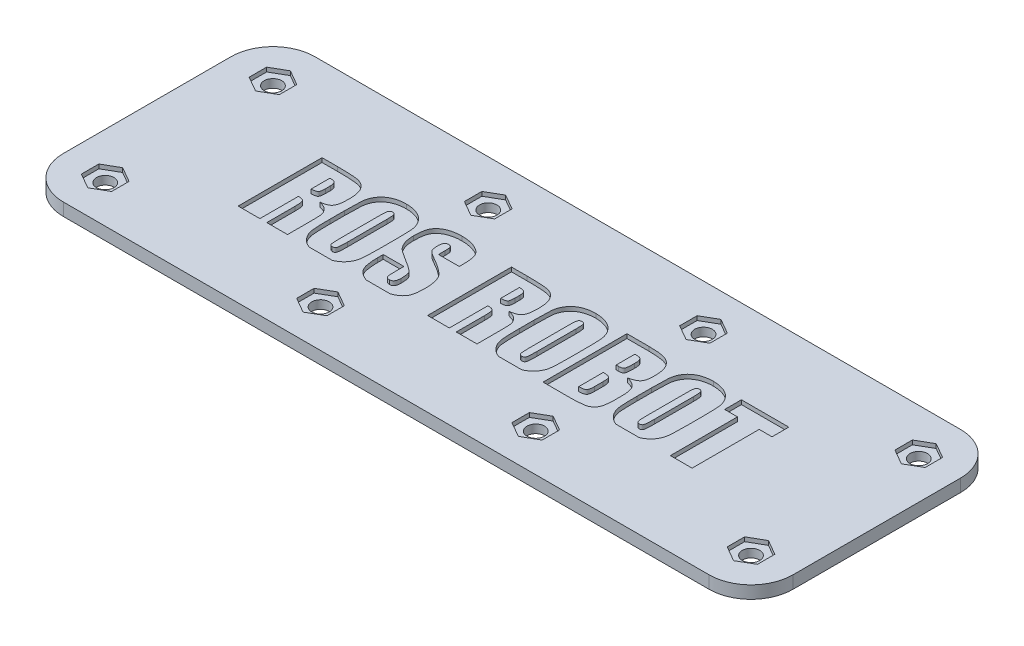
SolidWorks part; units mm, degrees
ref_plane "Front Plane" through (0, 0, 0) normal (0, 0, 1) x (1, 0, 0)
ref_plane "Top Plane" through (0, 0, 0) normal (0, 1, 0) x (1, 0, 0)
ref_plane "Right Plane" through (0, 0, 0) normal (1, 0, 0) x (0, 0, -1)
sketch "Sketch1" plane through (0, 0, 0) normal (0, 1, 0) x (1, 0, 0)
  line L1 (-87, 30) -> (87, 30)
  line L2 (-87, 30) -> (-87, -30)
  line L3 (-87, -30) -> (87, -30)
  line L4 (87, 30) -> (87, -30)
  line L5 (-87, 30) -> (87, -30) construction
  line L6 (-87, -30) -> (87, 30) construction
  point P0 (0, 0)
  dimension "D1" = 60
  dimension "D2" = 174
extrude "Boss-Extrude1" add sketch "Sketch1" along normal blind 3
sketch "Sketch2" plane through (0, 3, 0) normal (0, 1, 0) x (1, 0, 0)
  line L0 (-87, 30) -> (-87, -30) construction
  circle A0 centre (-76.995, 20) radius 2.09
  circle A1 centre (-25.665, 20) radius 2.09
  circle A2 centre (25.665, 20) radius 2.09
  circle A3 centre (76.995, 20) radius 2.09
  dimension "D1" = 4.18
  dimension "D2" = 4
  dimension "D3" = 10.005
  dimension "D4" = 20
extrude "Cut-Extrude1" cut sketch "Sketch2" against normal through all
mirror "Mirror1" about plane through (0, 0, 0) normal (0, 0, 1) of "Cut-Extrude1"
fillet "Fillet1" radius 10 4 edges at (-87, 1.5, 30) (87, 1.5, 30) (87, 1.5, -30) (-87, 1.5, -30)
sketch "Sketch3" plane through (0, 3, 0) normal (0, 1, 0) x (1, 0, 0)
  line L0 (-70, -10) -> (70, -10)
  line L1 (-55.2941, 10) -> (-51.5662, 10)
  line L2 (-43.5294, -4.6581) -> (-43.5294, -10)
  line L3 (-43.5294, -10) -> (-48.4706, -10)
  line L4 (-48.4706, -10) -> (-48.4706, -3.2353)
  line L5 (-50.1176, -0.8235) -> (-50.1176, -10)
  line L6 (-50.1176, -10) -> (-55.2941, -10)
  line L7 (-55.2941, -10) -> (-55.2941, 10)
  line L8 (-50.1176, 6.7059) -> (-50.1176, 2.2353)
  line L9 (-48.4706, 4.0478) -> (-48.4706, 5.1544)
  line L10 (-41.6471, -1.7206) -> (-41.6471, 1.7206)
  line L11 (-29.6471, 1.7206) -> (-29.6471, -1.7206)
  line L12 (-36.4706, 4.9596) -> (-36.4706, -4.5662)
  line L13 (-34.8235, -4.4154) -> (-34.8235, 4.9596)
  line L14 (-16.4706, 3.8824) -> (-21.4118, 3.8824)
  line L15 (-21.4118, 3.8824) -> (-21.4118, 5.4632)
  line L16 (-28, -4.0478) -> (-28, -2.7059)
  line L17 (-28, -2.7059) -> (-23.0588, -2.7059)
  line L18 (-23.0588, -2.7059) -> (-23.0588, -5.2978)
  line L19 (-16.4706, 4.6875) -> (-16.4706, 3.8824)
  line L20 (-10.1176, 10) -> (-6.3897, 10)
  line L21 (1.6471, -4.6581) -> (1.6471, -10)
  line L22 (1.6471, -10) -> (-3.2941, -10)
  line L23 (-3.2941, -10) -> (-3.2941, -3.2353)
  line L24 (-4.9412, -0.8235) -> (-4.9412, -10)
  line L25 (-4.9412, -10) -> (-10.1176, -10)
  line L26 (-10.1176, -10) -> (-10.1176, 10)
  line L27 (-4.9412, 6.7059) -> (-4.9412, 2.2353)
  line L28 (-3.2941, 4.0478) -> (-3.2941, 5.1544)
  line L29 (3.5294, -1.7206) -> (3.5294, 1.7206)
  line L30 (15.5294, 1.7206) -> (15.5294, -1.7206)
  line L31 (8.7059, 4.9596) -> (8.7059, -4.5662)
  line L32 (10.3529, -4.4154) -> (10.3529, 4.9596)
  line L33 (17.4118, 10) -> (22.7169, 10)
  line L34 (29.6471, -3.364) -> (29.6471, -5.2426)
  line L35 (23.4926, -10) -> (17.4118, -10)
  line L36 (17.4118, -10) -> (17.4118, 10)
  line L37 (22.5882, 6.7059) -> (22.5882, 2.2353)
  line L38 (22.5882, -0.8235) -> (22.5882, -6.7059)
  line L39 (24.4706, -4.7463) -> (24.4706, -2.7831)
  line L40 (31.5294, -1.7206) -> (31.5294, 1.7206)
  line L41 (43.5294, 1.7206) -> (43.5294, -1.7206)
  line L42 (36.7059, 4.9596) -> (36.7059, -4.5662)
  line L43 (38.3529, -4.4154) -> (38.3529, 4.9596)
  line L44 (56, 10) -> (56, 6)
  line L45 (56, 6) -> (52.9412, 6)
  line L46 (52.9412, 6) -> (52.9412, -10)
  line L47 (52.9412, -10) -> (47.7647, -10)
  line L48 (47.7647, -10) -> (47.7647, 6)
  line L49 (47.7647, 6) -> (44.7059, 6)
  line L50 (44.7059, 6) -> (44.7059, 10)
  line L51 (44.7059, 10) -> (56, 10)
  spline S0 degree 3 poles (-51.5662, 10) (-50.9938, 10.0021) (-50.1738, 9.9925) (-49.131, 9.9618) (-48.4616, 9.9343) (-47.8671, 9.8938) (-47.3485, 9.8469) (-46.9053, 9.7938) (-46.5265, 9.7279) (-46.1927, 9.6422) (-45.8846, 9.5296) (-45.5898, 9.3956) (-45.3117, 9.2282) (-45.0523, 9.0316) (-44.8023, 8.8156) (-44.5748, 8.5646) (-44.3559, 8.2904) (-44.158, 7.9777) (-43.9907, 7.6226) (-43.847, 7.2263) (-43.7305, 6.7869) (-43.6403, 6.3051) (-43.5478, 5.579) (-43.5348, 5.0099) (-43.5294, 4.6176) knots 0 0 0 0 0.148881 0.213303 0.271377 0.323138 0.368276 0.406827 0.439217 0.468212 0.496346 0.524443 0.552325 0.580569 0.609028 0.638128 0.668547 0.700209 0.734143 0.770448 0.80973 0.852244 0.897872 1 1 1 1
  spline S1 degree 3 poles (-43.5294, 4.6176) (-43.5236, 4.2653) (-43.5474, 3.7599) (-43.6025, 3.1182) (-43.671, 2.7076) (-43.7489, 2.3431) (-43.8469, 2.023) (-43.9667, 1.7514) (-44.1058, 1.5209) (-44.2744, 1.3269) (-44.4747, 1.1564) (-44.7132, 1.0108) (-44.9842, 0.8814) (-45.2896, 0.7718) (-45.7649, 0.6509) (-46.1435, 0.5949) (-46.4081, 0.5735) knots 0 0 0 0 0.18379 0.264137 0.336087 0.400976 0.458649 0.510492 0.555595 0.598692 0.64408 0.692369 0.744168 0.800637 0.861472 1 1 1 1
  spline S2 degree 3 poles (-46.4081, 0.5735) (-46.1692, 0.5082) (-45.8228, 0.4157) (-45.3924, 0.2537) (-45.1176, 0.1239) (-44.8709, -0.0075) (-44.6579, -0.1504) (-44.475, -0.3016) (-44.2801, -0.5089) (-44.0843, -0.7699) (-43.8891, -1.0747) (-43.748, -1.3697) (-43.6652, -1.6199) (-43.6287, -1.8463) (-43.5978, -2.0715) (-43.5791, -2.3577) (-43.5604, -2.7033) (-43.5466, -3.1078) (-43.5296, -3.7658) (-43.5348, -4.2893) (-43.5294, -4.6581) knots 0 0 0 0 0.11023 0.159227 0.204341 0.24532 0.283418 0.318243 0.350629 0.40972 0.463107 0.511383 0.554826 0.57974 0.613275 0.655917 0.707227 0.767226 0.835926 1 1 1 1
  spline S3 degree 3 poles (-48.4706, -3.2353) (-48.4728, -2.9891) (-48.4724, -2.639) (-48.5052, -2.1981) (-48.5325, -1.9256) (-48.5697, -1.6913) (-48.6105, -1.4957) (-48.6657, -1.339) (-48.7289, -1.2146) (-48.8113, -1.114) (-48.9232, -1.039) (-49.055, -0.9678) (-49.2166, -0.9133) (-49.4044, -0.8752) (-49.7069, -0.834) (-49.9484, -0.8249) (-50.1176, -0.8235) knots 0 0 0 0 0.208712 0.296135 0.374434 0.440653 0.497065 0.543362 0.580978 0.614872 0.652041 0.694298 0.741574 0.795735 0.856514 1 1 1 1
  spline S4 degree 3 poles (-50.1176, 2.2353) (-49.8576, 2.2338) (-49.4959, 2.2542) (-49.0697, 2.3585) (-48.8674, 2.4456) (-48.7457, 2.5571) (-48.6674, 2.6702) (-48.6082, 2.8204) (-48.5571, 3.0015) (-48.5182, 3.2158) (-48.4758, 3.5672) (-48.4762, 3.8494) (-48.4706, 4.0478) knots 0 0 0 0 0.26319 0.361521 0.442778 0.481273 0.526535 0.580255 0.643242 0.716208 0.799609 1 1 1 1
  spline S5 degree 3 poles (-48.4706, 5.1544) (-48.4732, 5.4183) (-48.4915, 5.7882) (-48.649, 6.209) (-48.8134, 6.422) (-49.0502, 6.5523) (-49.4796, 6.6913) (-49.8538, 6.7008) (-50.1176, 6.7059) knots 0 0 0 0 0.296724 0.405999 0.497474 0.590179 0.702697 1 1 1 1
  spline S6 degree 3 poles (-29.6471, -1.7206) (-29.6515, -2.1875) (-29.649, -2.8616) (-29.6628, -3.7232) (-29.6839, -4.2868) (-29.699, -4.7944) (-29.7259, -5.2478) (-29.7546, -5.6462) (-29.7961, -6.1016) (-29.8819, -6.6249) (-30.0686, -7.2195) (-30.3331, -7.7852) (-30.6652, -8.3214) (-31.0707, -8.8126) (-31.5464, -9.2461) (-32.0877, -9.6199) (-32.694, -9.9286) (-33.3578, -10.1686) (-34.3389, -10.4147) (-35.1174, -10.4641) (-35.6471, -10.4706) knots 0 0 0 0 0.112809 0.162854 0.208179 0.249065 0.285542 0.317902 0.345566 0.396043 0.445676 0.495616 0.546553 0.597656 0.649001 0.701564 0.75612 0.812885 0.871769 1 1 1 1
  spline S7 degree 3 poles (-35.6471, -10.4706) (-36.157, -10.4718) (-36.9063, -10.4086) (-37.8652, -10.1914) (-38.5237, -9.9594) (-39.1336, -9.6653) (-39.6789, -9.2941) (-40.1716, -8.8683) (-40.5862, -8.3693) (-40.9353, -7.8326) (-41.2061, -7.2648) (-41.3995, -6.6755) (-41.4957, -6.1587) (-41.5357, -5.7074) (-41.565, -5.3091) (-41.59, -4.8519) (-41.6129, -4.3384) (-41.6259, -3.766) (-41.6415, -2.8873) (-41.6458, -2.1985) (-41.6471, -1.7206) knots 0 0 0 0 0.123179 0.180929 0.237119 0.291548 0.344027 0.396062 0.448383 0.50021 0.550408 0.599943 0.649656 0.677029 0.709392 0.746168 0.787661 0.833574 0.884513 1 1 1 1
  spline S8 degree 3 poles (-41.6471, 1.7206) (-41.6425, 2.1887) (-41.6454, 2.8628) (-41.6311, 3.7244) (-41.6108, 4.2868) (-41.5934, 4.7954) (-41.5734, 5.2491) (-41.5426, 5.6473) (-41.5025, 6.102) (-41.4109, 6.6245) (-41.2257, 7.2194) (-40.9622, 7.7848) (-40.6264, 8.3182) (-40.225, 8.8141) (-39.7442, 9.2434) (-39.2063, 9.6217) (-38.599, 9.9269) (-37.9368, 10.1755) (-36.9518, 10.4071) (-36.1771, 10.476) (-35.6471, 10.4706) knots 0 0 0 0 0.1131 0.162847 0.20817 0.249054 0.28581 0.317873 0.345536 0.396062 0.445693 0.495631 0.546315 0.597643 0.649205 0.701523 0.756077 0.812942 0.872041 1 1 1 1
  spline S9 degree 3 poles (-35.6471, 10.4706) (-35.1376, 10.4697) (-34.3878, 10.4128) (-33.4319, 10.1862) (-32.7748, 9.9554) (-32.1629, 9.6647) (-31.6159, 9.2964) (-31.1263, 8.8668) (-30.7111, 8.3696) (-30.3634, 7.8316) (-30.0871, 7.2658) (-29.8946, 6.6743) (-29.798, 6.1563) (-29.7599, 5.7048) (-29.7225, 5.3082) (-29.7063, 4.8517) (-29.6803, 4.3385) (-29.6698, 3.7659) (-29.6434, 2.8875) (-29.6546, 2.1984) (-29.6471, 1.7206) knots 0 0 0 0 0.123202 0.180743 0.236944 0.291253 0.343988 0.395811 0.448142 0.499979 0.550314 0.59986 0.649873 0.677251 0.709348 0.746116 0.787617 0.833538 0.884493 1 1 1 1
  spline S10 degree 3 poles (-34.8235, 4.9596) (-34.8242, 5.1753) (-34.83, 5.4829) (-34.843, 5.8716) (-34.8622, 6.1155) (-34.8839, 6.3276) (-34.9074, 6.5086) (-34.9406, 6.6559) (-34.9862, 6.806) (-35.0702, 6.954) (-35.2687, 7.1431) (-35.486, 7.1725) (-35.6213, 7.1765) knots 0 0 0 0 0.245382 0.350014 0.44228 0.523563 0.592561 0.649714 0.69512 0.770679 0.840726 1 1 1 1
  spline S11 degree 3 poles (-35.6213, 7.1765) (-35.7476, 7.1828) (-35.9326, 7.1386) (-36.1407, 7.0007) (-36.2446, 6.8771) (-36.3135, 6.7446) (-36.354, 6.6034) (-36.3908, 6.4253) (-36.4175, 6.2075) (-36.4453, 5.9516) (-36.4612, 5.5307) (-36.473, 5.1963) (-36.4706, 4.9596) knots 0 0 0 0 0.141273 0.207934 0.278501 0.320511 0.375555 0.443281 0.525523 0.622695 0.733336 1 1 1 1
  spline S12 degree 3 poles (-36.4706, -4.5662) (-36.4661, -4.8346) (-36.4689, -5.2158) (-36.4552, -5.6951) (-36.4341, -5.9902) (-36.4194, -6.2432) (-36.3928, -6.4541) (-36.365, -6.6225) (-36.3252, -6.7864) (-36.2427, -6.9456) (-36.032, -7.1431) (-35.8027, -7.1757) (-35.6581, -7.1765) knots 0 0 0 0 0.263966 0.37491 0.47152 0.554902 0.624119 0.680394 0.722784 0.789642 0.853612 1 1 1 1
  spline S13 degree 3 poles (-35.6581, -7.1765) (-35.5065, -7.1791) (-35.2706, -7.1295) (-35.0575, -6.9077) (-34.9787, -6.7275) (-34.9317, -6.5458) (-34.9057, -6.3632) (-34.8796, -6.1401) (-34.8574, -5.8753) (-34.8447, -5.5687) (-34.8286, -5.0773) (-34.825, -4.6887) (-34.8235, -4.4154) knots 0 0 0 0 0.145036 0.209347 0.281953 0.327187 0.385478 0.455017 0.538188 0.634996 0.743262 1 1 1 1
  spline S14 degree 3 poles (-21.4118, 5.4632) (-21.4127, 5.7647) (-21.4197, 6.1714) (-21.5052, 6.6431) (-21.5927, 6.8638) (-21.7193, 7.0116) (-21.938, 7.1462) (-22.1365, 7.1803) (-22.2721, 7.1765) knots 0 0 0 0 0.412843 0.553103 0.65361 0.73318 0.814494 1 1 1 1
  spline S15 degree 3 poles (-22.2721, 7.1765) (-22.4224, 7.1753) (-22.6526, 7.1339) (-22.8986, 6.9564) (-23.0494, 6.7779) (-23.1638, 6.5473) (-23.267, 6.1427) (-23.3007, 5.8109) (-23.2941, 5.5735) knots 0 0 0 0 0.212113 0.312859 0.418563 0.535756 0.66915 1 1 1 1
  spline S16 degree 3 poles (-23.2941, 5.5735) (-23.2963, 5.2685) (-23.2666, 4.7355) (-23.1434, 4.2139) (-23.0441, 4.0074) knots 0 0 0 0 0.572651 1 1 1 1
  spline S17 degree 3 poles (-23.0441, 4.0074) (-22.9953, 3.9087) (-22.892, 3.7635) (-22.7165, 3.5783) (-22.5391, 3.4317) (-22.3344, 3.2741) (-21.9996, 3.0492) (-21.7223, 2.8928) (-21.5294, 2.7831) knots 0 0 0 0 0.166753 0.269572 0.387216 0.516182 0.662459 1 1 1 1
  spline S18 degree 3 poles (-21.5294, 2.7831) (-20.9703, 2.4734) (-20.1729, 2.0184) (-19.1897, 1.3881) (-18.5738, 0.9563) (-18.0389, 0.5522) (-17.4805, 0.0677) (-17.1194, -0.3024) (-16.9375, -0.5662) knots 0 0 0 0 0.335278 0.4813 0.612364 0.729739 0.832713 1 1 1 1
  spline S19 degree 3 poles (-16.9375, -0.5662) (-16.77, -0.806) (-16.5589, -1.2115) (-16.3573, -1.8106) (-16.226, -2.3243) (-16.1237, -2.8906) (-16.0244, -3.7446) (-16, -4.4137) (-16, -4.875) knots 0 0 0 0 0.195997 0.304678 0.423526 0.551406 0.690506 1 1 1 1
  spline S20 degree 3 poles (-16, -4.875) (-15.998, -5.2123) (-16.0141, -5.701) (-16.0695, -6.3269) (-16.1225, -6.7434) (-16.1969, -7.1236) (-16.2837, -7.469) (-16.3859, -7.7809) (-16.5079, -8.061) (-16.6548, -8.3173) (-16.8301, -8.5575) (-17.0323, -8.7896) (-17.2656, -9.0103) (-17.5281, -9.2213) (-17.8225, -9.4176) (-18.1454, -9.6065) (-18.6171, -9.8482) (-19.2609, -10.0984) (-20.3935, -10.3986) (-21.2929, -10.4667) (-21.9044, -10.4706) knots 0 0 0 0 0.107307 0.155459 0.199907 0.240819 0.278648 0.313174 0.345124 0.37569 0.406967 0.439576 0.4735 0.509002 0.546638 0.58596 0.627987 0.715167 0.805112 1 1 1 1
  spline S21 degree 3 poles (-21.9044, -10.4706) (-22.2484, -10.4757) (-22.7548, -10.4446) (-23.4141, -10.3628) (-23.8804, -10.2732) (-24.328, -10.1612) (-24.7555, -10.0192) (-25.1658, -9.8605) (-25.5494, -9.6676) (-25.9093, -9.4591) (-26.2396, -9.2368) (-26.5368, -8.9991) (-26.8027, -8.7496) (-27.0363, -8.4842) (-27.2339, -8.2027) (-27.4071, -7.9126) (-27.5395, -7.5995) (-27.6487, -7.2653) (-27.7465, -6.9026) (-27.8193, -6.5061) (-27.8876, -6.0774) (-27.9373, -5.6159) (-27.9879, -4.936) (-27.9998, -4.4094) (-28, -4.0478) knots 0 0 0 0 0.100145 0.147666 0.193464 0.238409 0.281993 0.324627 0.366464 0.406944 0.445764 0.482345 0.517706 0.551866 0.585155 0.617796 0.650099 0.683973 0.720175 0.759459 0.801374 0.84664 0.894618 1 1 1 1
  spline S22 degree 3 poles (-23.0588, -5.2978) (-23.0613, -5.4794) (-23.049, -5.7378) (-23.0335, -6.0657) (-23.0047, -6.2711) (-22.98, -6.4517) (-22.9371, -6.6031) (-22.8953, -6.7301) (-22.8277, -6.8628) (-22.7117, -6.9937) (-22.4544, -7.1506) (-22.2151, -7.1729) (-22.0551, -7.1765) knots 0 0 0 0 0.221449 0.31586 0.400263 0.474516 0.538003 0.591926 0.637412 0.719013 0.801608 1 1 1 1
  spline S23 degree 3 poles (-22.0551, -7.1765) (-21.8855, -7.181) (-21.6369, -7.1297) (-21.3606, -6.9481) (-21.2049, -6.755) (-21.0818, -6.5138) (-20.9682, -6.0948) (-20.9412, -5.7502) (-20.9412, -5.5074) knots 0 0 0 0 0.223296 0.324627 0.430189 0.546596 0.679609 1 1 1 1
  spline S24 degree 3 poles (-20.9412, -5.5074) (-20.9409, -5.2301) (-20.9533, -4.8334) (-21.0013, -4.3304) (-21.0575, -4.013) (-21.1206, -3.7324) (-21.2279, -3.4321) (-21.3302, -3.2311) (-21.4228, -3.125) knots 0 0 0 0 0.336674 0.481824 0.613234 0.728042 0.830673 1 1 1 1
  spline S25 degree 3 poles (-21.4228, -3.125) (-21.528, -3.0068) (-21.7234, -2.8316) (-22.0286, -2.599) (-22.3207, -2.3816) (-22.6652, -2.1468) (-23.2182, -1.7846) (-23.6661, -1.5149) (-23.9779, -1.3235) knots 0 0 0 0 0.151175 0.250667 0.367276 0.49971 0.649705 1 1 1 1
  spline S26 degree 3 poles (-23.9779, -1.3235) (-24.2945, -1.1313) (-24.7469, -0.8536) (-25.3157, -0.487) (-25.6766, -0.2459) (-25.9964, -0.028) (-26.2707, 0.1697) (-26.5041, 0.3453) (-26.7572, 0.5568) (-27.0307, 0.8386) (-27.3222, 1.2196) (-27.5825, 1.6572) (-27.8168, 2.1499) (-28.0109, 2.7079) (-28.187, 3.5918) (-28.2419, 4.2954) (-28.2353, 4.7868) knots 0 0 0 0 0.139497 0.199929 0.25485 0.30299 0.345648 0.382207 0.412998 0.469794 0.529711 0.593278 0.661207 0.734924 0.815133 1 1 1 1
  spline S27 degree 3 poles (-28.2353, 4.7868) (-28.2299, 5.1483) (-28.2229, 5.6721) (-28.1555, 6.342) (-28.0911, 6.7866) (-28.0062, 7.1929) (-27.9063, 7.5618) (-27.7803, 7.8893) (-27.6392, 8.183) (-27.4744, 8.4486) (-27.2854, 8.6932) (-27.0793, 8.9296) (-26.8428, 9.1431) (-26.5869, 9.3479) (-26.3089, 9.5388) (-26.0053, 9.711) (-25.5665, 9.9259) (-24.9651, 10.1466) (-23.8851, 10.4114) (-23.0241, 10.4702) (-22.4338, 10.4706) knots 0 0 0 0 0.115094 0.16642 0.214115 0.25793 0.298418 0.335563 0.369391 0.401957 0.434786 0.46765 0.501588 0.535991 0.571894 0.608743 0.64693 0.727243 0.81197 1 1 1 1
  spline S28 degree 3 poles (-22.4338, 10.4706) (-22.0994, 10.4657) (-21.6053, 10.4579) (-20.9648, 10.377) (-20.5106, 10.312) (-20.0772, 10.2133) (-19.6613, 10.1018) (-19.2659, 9.965) (-18.8924, 9.8068) (-18.5432, 9.6352) (-18.2193, 9.4575) (-17.9337, 9.2583) (-17.6686, 9.0613) (-17.4461, 8.8391) (-17.2428, 8.617) (-17.0786, 8.377) (-16.9405, 8.1223) (-16.8309, 7.8384) (-16.7307, 7.5198) (-16.6529, 7.1549) (-16.5815, 6.7482) (-16.5328, 6.2949) (-16.4819, 5.6039) (-16.471, 5.0626) (-16.4706, 4.6875) knots 0 0 0 0 0.103081 0.151694 0.198641 0.244219 0.288419 0.331125 0.37288 0.413199 0.450863 0.486435 0.520313 0.552325 0.583055 0.612876 0.641566 0.672036 0.706398 0.744284 0.786764 0.83346 0.884523 1 1 1 1
  spline S29 degree 3 poles (-6.3897, 10) (-5.8173, 10.0021) (-4.9973, 9.9925) (-3.9545, 9.9618) (-3.2851, 9.9343) (-2.6907, 9.8938) (-2.172, 9.8469) (-1.7288, 9.7938) (-1.3501, 9.7279) (-1.0162, 9.6422) (-0.7081, 9.5296) (-0.4133, 9.3956) (-0.1353, 9.2282) (0.1241, 9.0316) (0.3741, 8.8156) (0.6016, 8.5646) (0.8205, 8.2904) (1.0184, 7.9777) (1.1858, 7.6226) (1.3294, 7.2263) (1.4459, 6.7869) (1.5362, 6.3051) (1.6287, 5.579) (1.6416, 5.0099) (1.6471, 4.6176) knots 0 0 0 0 0.148881 0.213303 0.271377 0.323138 0.368276 0.406827 0.439217 0.468212 0.496346 0.524443 0.552325 0.580569 0.609028 0.638128 0.668547 0.700209 0.734143 0.770448 0.80973 0.852244 0.897872 1 1 1 1
  spline S30 degree 3 poles (1.6471, 4.6176) (1.6529, 4.2653) (1.629, 3.7599) (1.574, 3.1182) (1.5054, 2.7076) (1.4275, 2.3431) (1.3296, 2.023) (1.2098, 1.7514) (1.0707, 1.5209) (0.9021, 1.3269) (0.7018, 1.1564) (0.4633, 1.0108) (0.1923, 0.8814) (-0.1131, 0.7718) (-0.5885, 0.6509) (-0.9671, 0.5949) (-1.2316, 0.5735) knots 0 0 0 0 0.18379 0.264137 0.336087 0.400976 0.458649 0.510492 0.555595 0.598692 0.64408 0.692369 0.744168 0.800637 0.861472 1 1 1 1
  spline S31 degree 3 poles (-1.2316, 0.5735) (-0.9927, 0.5082) (-0.6463, 0.4157) (-0.2159, 0.2537) (0.0589, 0.1239) (0.3056, -0.0075) (0.5186, -0.1504) (0.7015, -0.3016) (0.8963, -0.5089) (1.0921, -0.7699) (1.2873, -1.0747) (1.4284, -1.3697) (1.5113, -1.6199) (1.5478, -1.8463) (1.5787, -2.0715) (1.5973, -2.3577) (1.6161, -2.7033) (1.6298, -3.1078) (1.6469, -3.7658) (1.6416, -4.2893) (1.6471, -4.6581) knots 0 0 0 0 0.11023 0.159227 0.204341 0.24532 0.283418 0.318243 0.350629 0.40972 0.463107 0.511383 0.554826 0.57974 0.613275 0.655917 0.707227 0.767226 0.835926 1 1 1 1
  spline S32 degree 3 poles (-3.2941, -3.2353) (-3.2963, -2.9891) (-3.2959, -2.639) (-3.3287, -2.1981) (-3.356, -1.9256) (-3.3932, -1.6913) (-3.434, -1.4957) (-3.4893, -1.339) (-3.5525, -1.2146) (-3.6348, -1.114) (-3.7468, -1.039) (-3.8785, -0.9678) (-4.0401, -0.9133) (-4.2279, -0.8752) (-4.5304, -0.834) (-4.7719, -0.8249) (-4.9412, -0.8235) knots 0 0 0 0 0.208712 0.296135 0.374434 0.440653 0.497065 0.543362 0.580978 0.614872 0.652041 0.694298 0.741574 0.795735 0.856514 1 1 1 1
  spline S33 degree 3 poles (-4.9412, 2.2353) (-4.6811, 2.2338) (-4.3195, 2.2542) (-3.8932, 2.3585) (-3.691, 2.4456) (-3.5692, 2.5571) (-3.491, 2.6702) (-3.4317, 2.8204) (-3.3807, 3.0015) (-3.3417, 3.2158) (-3.2993, 3.5672) (-3.2997, 3.8494) (-3.2941, 4.0478) knots 0 0 0 0 0.26319 0.361521 0.442778 0.481273 0.526535 0.580255 0.643242 0.716208 0.799609 1 1 1 1
  spline S34 degree 3 poles (-3.2941, 5.1544) (-3.2968, 5.4183) (-3.315, 5.7882) (-3.4725, 6.209) (-3.6369, 6.422) (-3.8737, 6.5523) (-4.3032, 6.6913) (-4.6773, 6.7008) (-4.9412, 6.7059) knots 0 0 0 0 0.296724 0.405999 0.497474 0.590179 0.702697 1 1 1 1
  spline S35 degree 3 poles (15.5294, -1.7206) (15.525, -2.1875) (15.5275, -2.8616) (15.5137, -3.7232) (15.4926, -4.2868) (15.4774, -4.7944) (15.4505, -5.2478) (15.4219, -5.6462) (15.3803, -6.1016) (15.2945, -6.6249) (15.1079, -7.2195) (14.8434, -7.7852) (14.5113, -8.3214) (14.1058, -8.8126) (13.6301, -9.2461) (13.0887, -9.6199) (12.4825, -9.9286) (11.8187, -10.1686) (10.8375, -10.4147) (10.059, -10.4641) (9.5294, -10.4706) knots 0 0 0 0 0.112809 0.162854 0.208179 0.249065 0.285542 0.317902 0.345566 0.396043 0.445676 0.495616 0.546553 0.597656 0.649001 0.701564 0.75612 0.812885 0.871769 1 1 1 1
  spline S36 degree 3 poles (9.5294, -10.4706) (9.0194, -10.4718) (8.2702, -10.4086) (7.3112, -10.1914) (6.6527, -9.9594) (6.0428, -9.6653) (5.4976, -9.2941) (5.0048, -8.8683) (4.5902, -8.3693) (4.2412, -7.8326) (3.9703, -7.2648) (3.777, -6.6755) (3.6808, -6.1587) (3.6408, -5.7074) (3.6114, -5.3091) (3.5864, -4.8519) (3.5636, -4.3384) (3.5505, -3.766) (3.535, -2.8873) (3.5307, -2.1985) (3.5294, -1.7206) knots 0 0 0 0 0.123179 0.180929 0.237119 0.291548 0.344027 0.396062 0.448383 0.50021 0.550408 0.599943 0.649656 0.677029 0.709392 0.746168 0.787661 0.833574 0.884513 1 1 1 1
  spline S37 degree 3 poles (3.5294, 1.7206) (3.534, 2.1887) (3.5311, 2.8628) (3.5454, 3.7244) (3.5657, 4.2868) (3.5831, 4.7954) (3.6031, 5.2491) (3.6338, 5.6473) (3.674, 6.102) (3.7656, 6.6245) (3.9507, 7.2194) (4.2143, 7.7848) (4.5501, 8.3182) (4.9514, 8.8141) (5.4322, 9.2434) (5.9701, 9.6217) (6.5774, 9.9269) (7.2397, 10.1755) (8.2247, 10.4071) (8.9993, 10.476) (9.5294, 10.4706) knots 0 0 0 0 0.1131 0.162847 0.20817 0.249054 0.28581 0.317873 0.345536 0.396062 0.445693 0.495631 0.546315 0.597643 0.649205 0.701523 0.756077 0.812942 0.872041 1 1 1 1
  spline S38 degree 3 poles (9.5294, 10.4706) (10.0389, 10.4697) (10.7887, 10.4128) (11.7445, 10.1862) (12.4016, 9.9554) (13.0135, 9.6647) (13.5606, 9.2964) (14.0502, 8.8668) (14.4654, 8.3696) (14.813, 7.8316) (15.0894, 7.2658) (15.2819, 6.6743) (15.3785, 6.1563) (15.4166, 5.7048) (15.4539, 5.3082) (15.4702, 4.8517) (15.4962, 4.3385) (15.5067, 3.7659) (15.5331, 2.8875) (15.5218, 2.1984) (15.5294, 1.7206) knots 0 0 0 0 0.123202 0.180743 0.236944 0.291253 0.343988 0.395811 0.448142 0.499979 0.550314 0.59986 0.649873 0.677251 0.709348 0.746116 0.787617 0.833538 0.884493 1 1 1 1
  spline S39 degree 3 poles (10.3529, 4.9596) (10.3523, 5.1753) (10.3464, 5.4829) (10.3334, 5.8716) (10.3143, 6.1155) (10.2926, 6.3276) (10.2691, 6.5086) (10.2359, 6.6559) (10.1902, 6.806) (10.1063, 6.954) (9.9078, 7.1431) (9.6905, 7.1725) (9.5551, 7.1765) knots 0 0 0 0 0.245382 0.350014 0.44228 0.523563 0.592561 0.649714 0.69512 0.770679 0.840726 1 1 1 1
  spline S40 degree 3 poles (9.5551, 7.1765) (9.4289, 7.1828) (9.2439, 7.1386) (9.0358, 7.0007) (8.9319, 6.8771) (8.8629, 6.7446) (8.8225, 6.6034) (8.7856, 6.4253) (8.759, 6.2075) (8.7312, 5.9516) (8.7153, 5.5307) (8.7035, 5.1963) (8.7059, 4.9596) knots 0 0 0 0 0.141273 0.207934 0.278501 0.320511 0.375555 0.443281 0.525523 0.622695 0.733336 1 1 1 1
  spline S41 degree 3 poles (8.7059, -4.5662) (8.7104, -4.8346) (8.7076, -5.2158) (8.7213, -5.6951) (8.7424, -5.9902) (8.7571, -6.2432) (8.7836, -6.4541) (8.8115, -6.6225) (8.8513, -6.7864) (8.9338, -6.9456) (9.1444, -7.1431) (9.3737, -7.1757) (9.5184, -7.1765) knots 0 0 0 0 0.263966 0.37491 0.47152 0.554902 0.624119 0.680394 0.722784 0.789642 0.853612 1 1 1 1
  spline S42 degree 3 poles (9.5184, -7.1765) (9.67, -7.1791) (9.9059, -7.1295) (10.119, -6.9077) (10.1978, -6.7275) (10.2447, -6.5458) (10.2708, -6.3632) (10.2969, -6.1401) (10.3191, -5.8753) (10.3318, -5.5687) (10.3479, -5.0773) (10.3515, -4.6887) (10.3529, -4.4154) knots 0 0 0 0 0.145036 0.209347 0.281953 0.327187 0.385478 0.455017 0.538188 0.634996 0.743262 1 1 1 1
  spline S43 degree 3 poles (22.7169, 10) (23.1103, 9.9955) (23.6819, 9.992) (24.4186, 9.9528) (24.9135, 9.9067) (25.3715, 9.8584) (25.7907, 9.7913) (26.1725, 9.7153) (26.5208, 9.6275) (26.8415, 9.5191) (27.1442, 9.3918) (27.4293, 9.2357) (27.6976, 9.0546) (27.9533, 8.8518) (28.1917, 8.6239) (28.4138, 8.3713) (28.6217, 8.094) (28.8126, 7.7825) (28.9734, 7.4264) (29.1074, 7.0267) (29.2229, 6.585) (29.3034, 6.0986) (29.3903, 5.3654) (29.4157, 4.791) (29.4118, 4.3934) knots 0 0 0 0 0.114402 0.166148 0.214441 0.258906 0.30003 0.337835 0.372059 0.404398 0.436167 0.46742 0.498748 0.530189 0.562197 0.59451 0.627862 0.662878 0.700507 0.741185 0.785348 0.833091 0.884404 1 1 1 1
  spline S44 degree 3 poles (29.4118, 4.3934) (29.4161, 4.127) (29.3961, 3.7432) (29.3352, 3.256) (29.279, 2.9367) (29.198, 2.6518) (29.1026, 2.3974) (28.9897, 2.1753) (28.854, 1.9816) (28.6904, 1.8122) (28.4956, 1.657) (28.2693, 1.5108) (28.006, 1.3797) (27.7137, 1.2484) (27.2525, 1.0966) (26.8888, 0.9936) (26.6324, 0.9412) knots 0 0 0 0 0.159593 0.229912 0.29415 0.353664 0.407126 0.456721 0.502563 0.548271 0.597357 0.65154 0.709345 0.77347 0.843372 1 1 1 1
  spline S45 degree 3 poles (26.6324, 0.9412) (26.9064, 0.8784) (27.3007, 0.7657) (27.7877, 0.563) (28.1067, 0.4024) (28.3887, 0.221) (28.6354, 0.0228) (28.849, -0.1912) (29.0238, -0.4284) (29.1732, -0.6877) (29.3023, -0.9756) (29.4066, -1.2968) (29.4955, -1.6492) (29.5643, -2.0325) (29.6289, -2.6073) (29.6457, -3.0548) (29.6471, -3.364) knots 0 0 0 0 0.144065 0.209342 0.269975 0.326732 0.380744 0.431785 0.481119 0.531179 0.584839 0.642399 0.7039 0.770874 0.841644 1 1 1 1
  spline S46 degree 3 poles (29.6471, -5.2426) (29.6469, -5.5627) (29.635, -6.0268) (29.585, -6.6223) (29.5342, -7.0199) (29.4687, -7.3845) (29.3885, -7.7163) (29.2938, -8.0154) (29.1496, -8.3632) (28.9276, -8.7469) (28.5806, -9.1307) (28.1655, -9.4378) (27.7574, -9.6247) (27.3756, -9.7329) (27.0179, -9.8055) (26.5945, -9.8667) (26.1022, -9.9115) (25.5458, -9.9523) (24.6684, -9.994) (23.9767, -9.9946) (23.4926, -10) knots 0 0 0 0 0.10225 0.148225 0.190863 0.23026 0.266534 0.299842 0.330381 0.386718 0.440498 0.49453 0.550588 0.582802 0.621196 0.667098 0.719418 0.779086 0.845327 1 1 1 1
  spline S47 degree 2 poles (22.5882, 2.2353) (22.875, 2.243) (23.1618, 2.2463) knots 0 0 0 1 1 1
  spline S48 degree 3 poles (23.1618, 2.2463) (23.394, 2.2431) (23.7204, 2.2711) (24.0836, 2.4402) (24.2309, 2.5926) (24.3018, 2.7538) (24.3482, 2.9156) (24.3821, 3.1219) (24.4157, 3.3706) (24.4401, 3.6651) (24.4654, 4.1442) (24.4705, 4.5257) (24.4706, 4.7941) knots 0 0 0 0 0.207123 0.283932 0.350841 0.389257 0.439129 0.499893 0.574453 0.661745 0.761896 1 1 1 1
  spline S49 degree 3 poles (24.4706, 4.7941) (24.4725, 5.0632) (24.4561, 5.4327) (24.3771, 5.876) (24.291, 6.1089) (24.1851, 6.2879) (24.0656, 6.4274) (23.9321, 6.5346) (23.7711, 6.6046) (23.5692, 6.647) (23.172, 6.6936) (22.8358, 6.7017) (22.5882, 6.7059) knots 0 0 0 0 0.247893 0.340016 0.413628 0.475403 0.53064 0.582138 0.631667 0.690827 0.771639 1 1 1 1
  spline S50 degree 3 poles (22.5882, -6.7059) (22.7721, -6.6974) (23.0359, -6.6865) (23.3661, -6.639) (23.5743, -6.6004) (23.7547, -6.5485) (23.9092, -6.4911) (24.0376, -6.4263) (24.1395, -6.3453) (24.2198, -6.2425) (24.2905, -6.117) (24.343, -5.9579) (24.3904, -5.7726) (24.4267, -5.5574) (24.4604, -5.2128) (24.4753, -4.9391) (24.4706, -4.7463) knots 0 0 0 0 0.168587 0.241054 0.305045 0.362185 0.41258 0.455716 0.49319 0.530665 0.574337 0.624343 0.683356 0.749349 0.823768 1 1 1 1
  spline S51 degree 3 poles (24.4706, -2.7831) (24.4699, -2.581) (24.4683, -2.2928) (24.427, -1.9325) (24.4043, -1.7098) (24.3567, -1.5228) (24.3088, -1.3668) (24.2464, -1.244) (24.1737, -1.147) (24.0747, -1.0775) (23.9541, -1.0154) (23.7998, -0.9656) (23.6165, -0.9226) (23.4028, -0.8865) (23.0575, -0.8455) (22.7821, -0.8306) (22.5882, -0.8235) knots 0 0 0 0 0.18245 0.259089 0.327073 0.383894 0.432816 0.473837 0.507662 0.540813 0.581834 0.629709 0.686529 0.751567 0.825033 1 1 1 1
  spline S52 degree 3 poles (43.5294, -1.7206) (43.525, -2.1875) (43.5275, -2.8616) (43.5137, -3.7232) (43.4926, -4.2868) (43.4774, -4.7944) (43.4505, -5.2478) (43.4219, -5.6462) (43.3803, -6.1016) (43.2945, -6.6249) (43.1079, -7.2195) (42.8434, -7.7852) (42.5113, -8.3214) (42.1058, -8.8126) (41.6301, -9.2461) (41.0887, -9.6199) (40.4825, -9.9286) (39.8187, -10.1686) (38.8375, -10.4147) (38.059, -10.4641) (37.5294, -10.4706) knots 0 0 0 0 0.112809 0.162854 0.208179 0.249065 0.285542 0.317902 0.345566 0.396043 0.445676 0.495616 0.546553 0.597656 0.649001 0.701564 0.75612 0.812885 0.871769 1 1 1 1
  spline S53 degree 3 poles (37.5294, -10.4706) (37.0194, -10.4718) (36.2702, -10.4086) (35.3112, -10.1914) (34.6527, -9.9594) (34.0428, -9.6653) (33.4976, -9.2941) (33.0048, -8.8683) (32.5902, -8.3693) (32.2412, -7.8326) (31.9703, -7.2648) (31.777, -6.6755) (31.6808, -6.1587) (31.6408, -5.7074) (31.6114, -5.3091) (31.5864, -4.8519) (31.5636, -4.3384) (31.5505, -3.766) (31.535, -2.8873) (31.5307, -2.1985) (31.5294, -1.7206) knots 0 0 0 0 0.123179 0.180929 0.237119 0.291548 0.344027 0.396062 0.448383 0.50021 0.550408 0.599943 0.649656 0.677029 0.709392 0.746168 0.787661 0.833574 0.884513 1 1 1 1
  spline S54 degree 3 poles (31.5294, 1.7206) (31.534, 2.1887) (31.5311, 2.8628) (31.5454, 3.7244) (31.5657, 4.2868) (31.5831, 4.7954) (31.6031, 5.2491) (31.6338, 5.6473) (31.674, 6.102) (31.7656, 6.6245) (31.9507, 7.2194) (32.2143, 7.7848) (32.5501, 8.3182) (32.9514, 8.8141) (33.4322, 9.2434) (33.9701, 9.6217) (34.5774, 9.9269) (35.2397, 10.1755) (36.2247, 10.4071) (36.9993, 10.476) (37.5294, 10.4706) knots 0 0 0 0 0.1131 0.162847 0.20817 0.249054 0.28581 0.317873 0.345536 0.396062 0.445693 0.495631 0.546315 0.597643 0.649205 0.701523 0.756077 0.812942 0.872041 1 1 1 1
  spline S55 degree 3 poles (37.5294, 10.4706) (38.0389, 10.4697) (38.7887, 10.4128) (39.7445, 10.1862) (40.4016, 9.9554) (41.0135, 9.6647) (41.5606, 9.2964) (42.0502, 8.8668) (42.4654, 8.3696) (42.813, 7.8316) (43.0894, 7.2658) (43.2819, 6.6743) (43.3785, 6.1563) (43.4166, 5.7048) (43.4539, 5.3082) (43.4702, 4.8517) (43.4962, 4.3385) (43.5067, 3.7659) (43.5331, 2.8875) (43.5218, 2.1984) (43.5294, 1.7206) knots 0 0 0 0 0.123202 0.180743 0.236944 0.291253 0.343988 0.395811 0.448142 0.499979 0.550314 0.59986 0.649873 0.677251 0.709348 0.746116 0.787617 0.833538 0.884493 1 1 1 1
  spline S56 degree 3 poles (38.3529, 4.9596) (38.3523, 5.1753) (38.3464, 5.4829) (38.3334, 5.8716) (38.3143, 6.1155) (38.2926, 6.3276) (38.2691, 6.5086) (38.2359, 6.6559) (38.1902, 6.806) (38.1063, 6.954) (37.9078, 7.1431) (37.6905, 7.1725) (37.5551, 7.1765) knots 0 0 0 0 0.245382 0.350014 0.44228 0.523563 0.592561 0.649714 0.69512 0.770679 0.840726 1 1 1 1
  spline S57 degree 3 poles (37.5551, 7.1765) (37.4289, 7.1828) (37.2439, 7.1386) (37.0358, 7.0007) (36.9319, 6.8771) (36.8629, 6.7446) (36.8225, 6.6034) (36.7856, 6.4253) (36.759, 6.2075) (36.7312, 5.9516) (36.7153, 5.5307) (36.7035, 5.1963) (36.7059, 4.9596) knots 0 0 0 0 0.141273 0.207934 0.278501 0.320511 0.375555 0.443281 0.525523 0.622695 0.733336 1 1 1 1
  spline S58 degree 3 poles (36.7059, -4.5662) (36.7104, -4.8346) (36.7076, -5.2158) (36.7213, -5.6951) (36.7424, -5.9902) (36.7571, -6.2432) (36.7836, -6.4541) (36.8115, -6.6225) (36.8513, -6.7864) (36.9338, -6.9456) (37.1444, -7.1431) (37.3737, -7.1757) (37.5184, -7.1765) knots 0 0 0 0 0.263966 0.37491 0.47152 0.554902 0.624119 0.680394 0.722784 0.789642 0.853612 1 1 1 1
  spline S59 degree 3 poles (37.5184, -7.1765) (37.67, -7.1791) (37.9059, -7.1295) (38.119, -6.9077) (38.1978, -6.7275) (38.2447, -6.5458) (38.2708, -6.3632) (38.2969, -6.1401) (38.3191, -5.8753) (38.3318, -5.5687) (38.3479, -5.0773) (38.3515, -4.6887) (38.3529, -4.4154) knots 0 0 0 0 0.145036 0.209347 0.281953 0.327187 0.385478 0.455017 0.538188 0.634996 0.743262 1 1 1 1
  point P2 (0, -10)
  dimension "D1" = 10
  dimension "D2" = 140
extrude "Cut-Extrude2" cut sketch "Sketch3" against normal blind 1 contours S3 L4 L0 L2 S2 S1 S0 L1 L7 L5 S5 L9 S4 L8 | S9 S8 L10 S7 L0 S6 L11 S13 S12 L12 S11 S10 L13 | S28 S27 S26 S25 S24 S23 S22 L18 L17 L16 S21 L0 S20 S19 S18 S17 S16 S15 S14 L15 L14 L19 | S32 L23 L0 L21 S31 S30 S29 L20 L26 L24 S34 L28 S33 L27 | S38 S37 L29 S36 L0 S35 L30 S42 S41 L31 S40 S39 L32 | S46 L34 S45 S44 S43 L33 L36 L0 S51 L39 S50 L38 S49 S48 S47 L37 | S55 S54 L40 S53 L0 S52 L41 S59 S58 L42 S57 S56 L43 | L51 L50 L49 L48 L0 L46 L45 L44
sketch "Sketch4" plane through (0, 3, 0) normal (0, 1, 0) x (1, 0, 0)
  line L0 (-87, 20) -> (-87, -20) construction
  line L1 (-76.995, 15.8431) -> (-73.395, 17.9215)
  line L2 (-73.395, 17.9215) -> (-73.395, 22.0785)
  line L3 (-73.395, 22.0785) -> (-76.995, 24.1569)
  line L4 (-76.995, 24.1569) -> (-80.595, 22.0785)
  line L5 (-80.595, 22.0785) -> (-80.595, 17.9215)
  line L6 (-80.595, 17.9215) -> (-76.995, 15.8431)
  line L7 (-25.665, 15.8431) -> (-22.065, 17.9215)
  line L8 (-22.065, 17.9215) -> (-22.065, 22.0785)
  line L9 (-22.065, 22.0785) -> (-25.665, 24.1569)
  line L10 (-25.665, 24.1569) -> (-29.265, 22.0785)
  line L11 (-29.265, 22.0785) -> (-29.265, 17.9215)
  line L12 (-29.265, 17.9215) -> (-25.665, 15.8431)
  line L13 (25.665, 15.8431) -> (29.265, 17.9215)
  line L14 (29.265, 17.9215) -> (29.265, 22.0785)
  line L15 (29.265, 22.0785) -> (25.665, 24.1569)
  line L16 (25.665, 24.1569) -> (22.065, 22.0785)
  line L17 (22.065, 22.0785) -> (22.065, 17.9215)
  line L18 (22.065, 17.9215) -> (25.665, 15.8431)
  line L19 (76.995, 15.8431) -> (80.595, 17.9215)
  line L20 (80.595, 17.9215) -> (80.595, 22.0785)
  line L21 (80.595, 22.0785) -> (76.995, 24.1569)
  line L22 (76.995, 24.1569) -> (73.395, 22.0785)
  line L23 (73.395, 22.0785) -> (73.395, 17.9215)
  line L24 (73.395, 17.9215) -> (76.995, 15.8431)
  circle A0 centre (-76.995, 20) radius 3.6 construction
  circle A1 centre (-76.995, 20) radius 2.09 construction
  dimension "D1" = 7.2
  dimension "D2" = 4
extrude "Cut-Extrude3" cut sketch "Sketch4" against normal blind 1
mirror "Mirror2" about plane through (0, 0, 0) normal (0, 0, 1) of "Cut-Extrude3"
